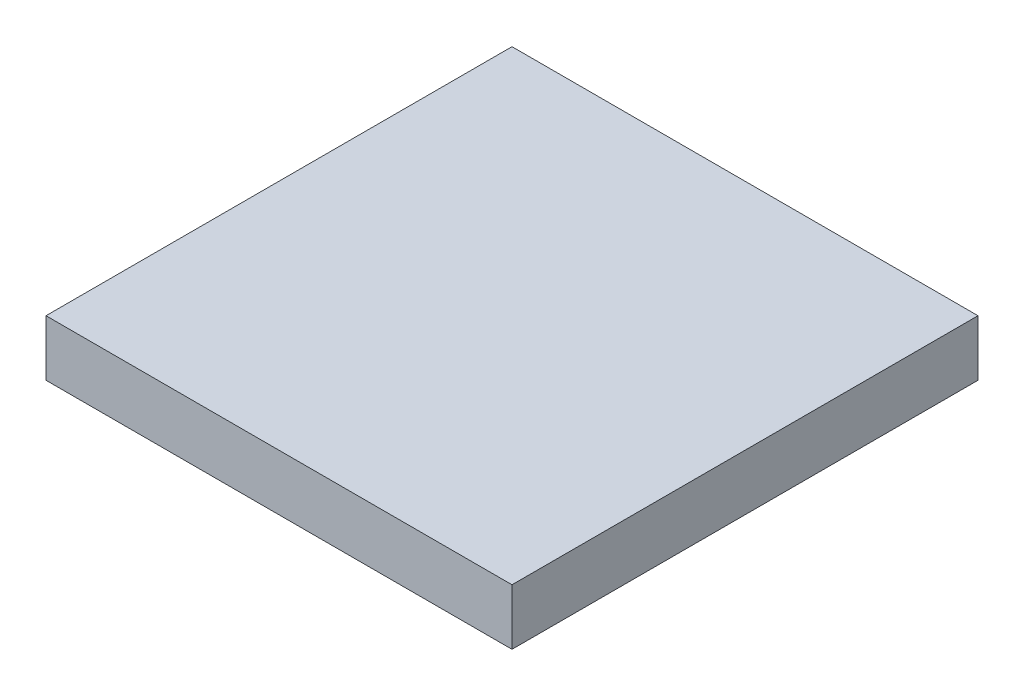
SolidWorks part; units mm, degrees
ref_plane "Front Plane" through (0, 0, 0) normal (0, 0, 1) x (1, 0, 0)
ref_plane "Top Plane" through (0, 0, 0) normal (0, 1, 0) x (1, 0, 0)
ref_plane "Right Plane" through (0, 0, 0) normal (1, 0, 0) x (0, 0, -1)
sketch "Sketch1" plane through (0, 0, 0) normal (0, 1, 0) x (1, 0, 0)
  line L1 (-12.5, -12.5) -> (12.5, -12.5)
  line L2 (-12.5, -12.5) -> (-12.5, 12.5)
  line L3 (-12.5, 12.5) -> (12.5, 12.5)
  line L4 (12.5, -12.5) -> (12.5, 12.5)
  line L5 (-12.5, -12.5) -> (12.5, 12.5) construction
  line L6 (-12.5, 12.5) -> (12.5, -12.5) construction
  point P0 (0, 0)
  dimension "D1" = 25
  dimension "D2" = 25
extrude "Boss-Extrude1" add sketch "Sketch1" along normal blind 3
sketch "Sketch2" plane through (0, 0, 0) normal (0, -1, 0) x (1, 0, 0)
  line L1 (-10, -10) -> (10, -10)
  line L2 (-10, -10) -> (-10, 10)
  line L3 (-10, 10) -> (10, 10)
  line L4 (10, -10) -> (10, 10)
  line L5 (-10, -10) -> (10, 10) construction
  line L6 (-10, 10) -> (10, -10) construction
  circle A0 centre (0, 0) radius 5
  point P0 (0, 0)
  dimension "D3" = 10
  dimension "D1" = 20
  dimension "D2" = 20
extrude "Cut-Extrude1" cut sketch "Sketch2" against normal blind 2
sketch "Sketch3" plane through (0, 0, 0) normal (0, -1, 0) x (1, 0, 0)
  line L0 (12.5, -12.5) -> (-12.5, -12.5) construction
  line L1 (-12.5, -12.5) -> (-12.5, 12.5) construction
  line L2 (-12.5, 12.5) -> (12.5, 12.5) construction
  line L3 (12.5, 12.5) -> (12.5, -12.5) construction
  circle A0 centre (-11, 11) radius 1.25
  circle A1 centre (11, 11) radius 1.25
  circle A2 centre (11, -11) radius 1.25
  circle A3 centre (-11, -11) radius 1.25
  dimension "D1" = 2.5
  dimension "D4" = 2.5
  dimension "D7" = 2.5
  dimension "D10" = 2.5
  dimension "D2" = 1.5
  dimension "D3" = 1.5
  dimension "D5" = 1.5
  dimension "D6" = 1.5
  dimension "D8" = 1.5
  dimension "D9" = 1.5
  dimension "D11" = 1.5
  dimension "D12" = 1.5
extrude "Cut-Extrude2" cut sketch "Sketch3" against normal blind 2
